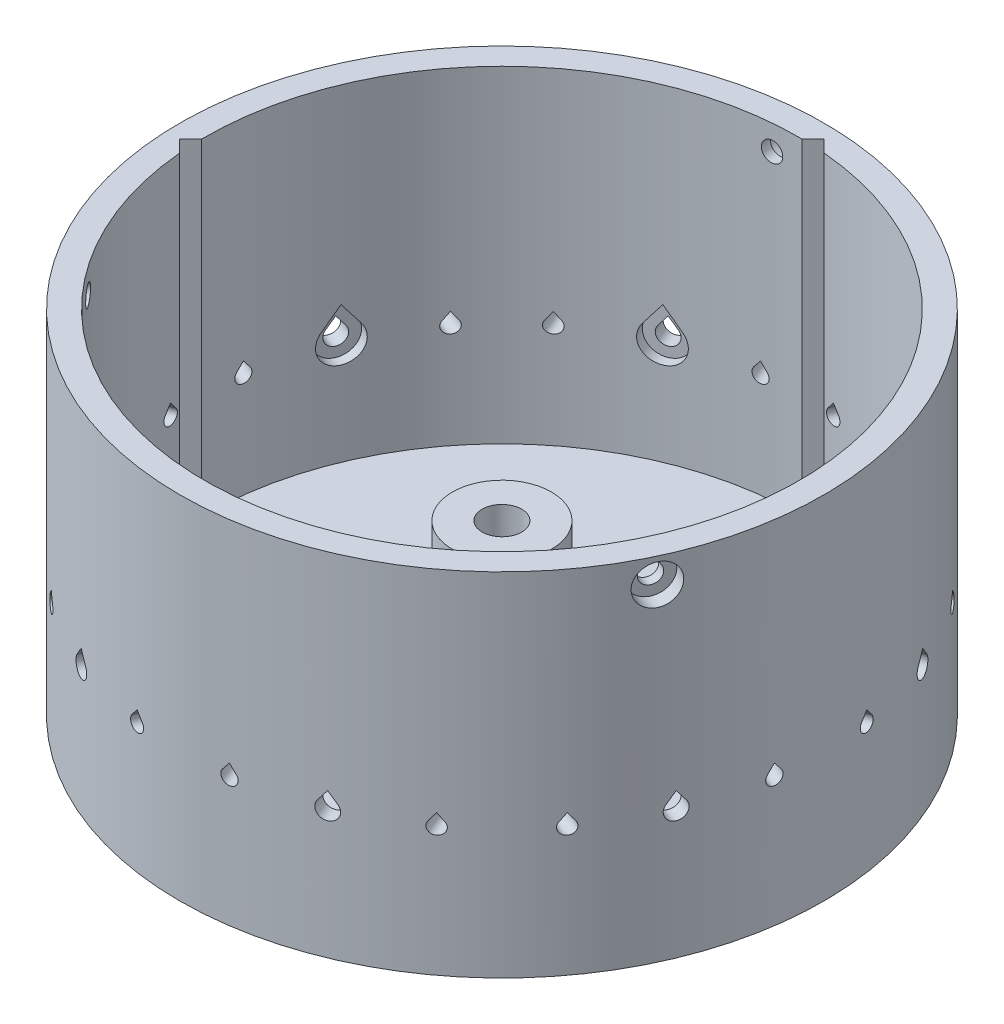
SolidWorks part; units mm, degrees
ref_plane "Front Plane" through (0, 0, 0) normal (0, 0, 1) x (1, 0, 0)
ref_plane "Top Plane" through (0, 0, 0) normal (0, 1, 0) x (1, 0, 0)
ref_plane "Right Plane" through (0, 0, 0) normal (1, 0, 0) x (0, 0, -1)
sketch "Sketch1" plane through (0, 0, 0) normal (0, 0, 1) x (1, 0, 0)
  line L0 (120, 0) -> (156, 0)
  line L1 (148, -36) -> (120, -36)
  line L2 (120, -36) -> (120, 0)
  line L3 (0, 0) -> (0, -64.9986) construction
  arc A0 (156, 0) -> (160, -4) centre (156, -4) cw
  arc A1 (160, -4) -> (151.3962, -34.1132) centre (103, -4) cw
  arc A2 (151.3962, -34.1132) -> (148, -36) centre (148, -32) cw
  dimension "D5" = 4
  dimension "D6" = 4
  dimension "D1" = 160
  dimension "D2" = 40
  dimension "D3" = 36
  dimension "D4" = 28
revolve "Revolve1" add sketch "Sketch1" angle 360 about L3
sketch "Sketch5" plane through (0, 0, 0) normal (1, 0, 0) x (0, 0, -1)
  line L0 (60, 0) -> (65, 0)
  line L1 (65, -71) -> (60, -71)
  line L2 (120, 0) -> (-120, 0) construction
  line L3 (0, 16.2431) -> (0, -72.818) construction
  line L4 (65, 0) -> (65, -31)
  line L5 (60, 0) -> (60, -71)
  line L6 (-148, -36) -> (148, -36) construction
  line L8 (65, -36) -> (65, -71)
  line L9 (65, -31) -> (81, -31)
  line L11 (65, -36) -> (81, -36)
  line L12 (81, -31) -> (81, -36)
  dimension "D1" = 65
  dimension "D2" = 5
  dimension "D3" = 90
  dimension "D4" = 35
  dimension "D5" = 5
  dimension "D6" = 16
revolve "Revolve2" add sketch "Sketch5" angle 360 about L3
sketch "Sketch6" plane through (0, 0, 0) normal (1, 0, 0) x (0, 0, -1)
  line L0 (-16, -33.5) -> (16, -33.5) construction
  line L1 (0, -33.5) -> (0, 18.5493) construction
  line L3 (-148, -36) -> (148, -36) construction
  circle A0 centre (-16, -33.5) radius 2.5
  circle A1 centre (16, -33.5) radius 2.5
  dimension "D1" = 5
  dimension "D2" = 16
extrude "Boss-Extrude1" add sketch "Sketch6" along normal up to surface and the other way up to surface
sketch "Sketch7" plane through (0, 0, 0) normal (0, 0, 1) x (1, 0, 0)
  line L0 (0, -60.0786) -> (0, 55.372) construction
pattern_circular "CirPattern2" count 4 every 45 about axis through (0, -60.0786, 0) along (0, 1, 0) of "Boss-Extrude1"
sketch "Sketch8" plane through (0, 0, 0) normal (0, 0, 1) x (1, 0, 0)
  line L0 (0, 0) -> (0, -91.6865)
  line L1 (0, -91.6865) -> (-49.5238, -91.6865)
  line L2 (-49.5238, -91.6865) -> (-60, -71)
  line L3 (-60, 0) -> (0, 0)
  line L4 (-60, 0) -> (-60, -71)
revolve "Cut-Revolve1" cut sketch "Sketch8" angle 360 about L0
sketch "Sketch9" plane through (0, -71, 0) normal (0, -1, 0) x (1, 0, 0)
  circle A0 centre (0, 0) radius 60
  circle A1 centre (0, 0) radius 60 construction
extrude "Boss-Extrude2" add sketch "Sketch9" against normal blind 5
sketch "Sketch10" plane through (0, -71, 0) normal (0, -1, 0) x (1, 0, 0)
  circle A0 centre (0, 0) radius 15
  dimension "D1" = 30
extrude "Cut-Extrude1" cut sketch "Sketch10" against normal up to next
sketch "Sketch11" plane through (0, 0, 0) normal (1, 0, 0) x (0, 0, -1)
  line L0 (0, -71) -> (0, 0) construction
  line L1 (-65, -71) -> (65, -71) construction
  line L3 (-7.3604, -71) -> (-4, -71)
  line L4 (-4, -71) -> (-4, -37)
  line L5 (-4, -37) -> (-8.0477, -37)
  line L7 (-8.0477, -37) -> (-10, -37)
  line L8 (-10, -37) -> (-10, -66)
  line L9 (-10, -66) -> (-15, -66)
  line L10 (-15, -66) -> (-15, -71)
  line L11 (-15, -71) -> (-7.3604, -71)
  line L12 (15, -66) -> (-15, -66) construction
  dimension "D1" = 34
  dimension "D3" = 20
  dimension "D4" = 8
revolve "Revolve3" add sketch "Sketch11" angle 360 about L0
sketch "Sketch14" plane through (0, 0, 0) normal (0, 1, 0) x (1, 0, 0)
  line L0 (2.8284, 62.2254) -> (-62.2254, -2.8284)
  line L1 (-62.2254, -2.8284) -> (-58.6899, -6.364)
  line L2 (-58.6899, -6.364) -> (6.364, 58.6899)
  line L3 (6.364, 58.6899) -> (2.8284, 62.2254)
  line L4 (0, 0) -> (-26.163, 26.163) construction
  line L5 (0, 0) -> (0, 27.5033) construction
  dimension "D1" = 45
  dimension "D2" = 92
  dimension "D3" = 5
  dimension "D4" = 42
extrude "Cut-Extrude3" cut sketch "Sketch14" against normal up to surface (66 mm away) up to face at (0, -66, -60)
sketch "Sketch17" plane through (0, -36, 0) normal (0, -1, 0) x (1, 0, 0)
  circle A0 centre (0, 0) radius 65
  circle A1 centre (0, 0) radius 160
  circle A2 centre (0, 0) radius 160 construction
  circle A3 centre (0, 0) radius 65 construction
extrude "Cut-Extrude4" cut sketch "Sketch17" against normal through all
ref_plane "Plane1" through (-60.0522, 0, 24.8744) normal (-0.9239, 0, 0.3827) x (0.3827, 0, 0.9239)
ref_plane "Plane2" through (-50.8134, 0, 21.0476) normal (-0.9239, 0, 0.3827) x (0.3827, 0, 0.9239)
sketch "Sketch18" plane through (-60.0522, 0, 24.8744) normal (-0.9239, 0, 0.3827) x (0.3827, 0, 0.9239)
  line L0 (65, 0) -> (-65, 0) construction
  line L1 (0, 0) -> (0, -45) construction
  line L2 (16, -45) -> (0, -45) construction
  line L3 (0, -45) -> (-16, -45) construction
  line L4 (-17.19, -44.0869) -> (-16, -42.536)
  line L5 (-16, -42.536) -> (-14.81, -44.0869)
  line L6 (-1.5867, -43.7825) -> (0, -41.7146)
  line L7 (0, -41.7146) -> (1.5867, -43.7825)
  line L8 (14.81, -44.0869) -> (16, -42.536)
  line L9 (16, -42.536) -> (17.19, -44.0869)
  line L10 (-16, -42.536) -> (-16, -45) construction
  line L11 (16, -42.536) -> (16, -45) construction
  arc A0 (-1.5867, -43.7825) -> (1.5867, -43.7825) centre (0, -45) ccw
  arc A1 (-17.19, -44.0869) -> (-14.81, -44.0869) centre (-16, -45) ccw
  arc A2 (14.81, -44.0869) -> (17.19, -44.0869) centre (16, -45) ccw
  dimension "D1" = 4
  dimension "D3" = 3
  dimension "D4" = 32
  dimension "D2" = 45
  dimension "D5" = 75
  dimension "D6" = 75
  dimension "D7" = 75
extrude "Cut-Extrude5" cut sketch "Sketch18" against normal up to next
sketch "Sketch20" plane through (-50.8134, 0, 21.0476) normal (-0.9239, 0, 0.3827) x (0.3827, 0, 0.9239)
  line L0 (-3.1734, -42.565) -> (0, -38.4293)
  line L1 (0, -38.4293) -> (3.1734, -42.565)
  line L2 (0, -45) -> (0, -38.4293) construction
  arc A0 (-3.1734, -42.565) -> (3.1734, -42.565) centre (0, -45) ccw
  dimension "D1" = 8
  dimension "D2" = 75
extrude "Cut-Extrude6" cut sketch "Sketch20" along normal blind 7
pattern_circular "CirPattern3" count 8 over 360 about axis through (0, 0, 0) along (0, 1, 0) of "Cut-Extrude5", "Cut-Extrude6"
ref_plane "Plane4" through (9.0631, 0, 4.2262) normal (0.9063, 0, 0.4226) x (0.4226, 0, -0.9063)
sketch "Sketch22" plane through (20.043, 0, -19.3204) normal (-0.9063, 0, -0.4226) x (-0.4226, 0, 0.9063)
  line L0 (25.9808, 0) -> (25.9808, -5) construction
  circle A0 centre (25.9808, -5) radius 2
  dimension "D1" = 4
  dimension "D2" = 5
extrude "Cut-Extrude8" cut sketch "Sketch22" against normal through all
ref_plane "Plane3" through (58.91, 0, 27.4702) normal (0.9063, 0, 0.4226) x (0.4226, 0, -0.9063)
sketch "Sketch23" plane through (58.91, 0, 27.4702) normal (0.9063, 0, 0.4226) x (0.4226, 0, -0.9063)
  circle A0 centre (0, -5) radius 4
  dimension "D1" = 8
extrude "Cut-Extrude9" cut sketch "Sketch23" against normal blind 3
pattern_circular "CirPattern4" count 3 over 360 about axis through (0, 0, 0) along (0, 1, 0) of "Cut-Extrude8", "Cut-Extrude9"
sketch "Sketch26" plane through (0, -71, 0) normal (0, -1, 0) x (1, 0, 0)
  line L0 (-25.9808, 15) -> (-2.2721, 15)
  line L1 (-2.2721, 15) -> (-13.8721, 26.6001)
  circle A0 centre (0, 0) radius 15 construction
  circle A1 centre (0, 0) radius 30 construction
  arc A2 (-13.8721, 26.6001) -> (-25.9808, 15) centre (0, 0) ccw
  dimension "D1" = 30
  dimension "D2" = 60
  dimension "D3" = 45
  dimension "D4" = 15
  dimension "D5" = 9
extrude "Cut-Extrude12" cut sketch "Sketch26" against normal up to next (5 mm away)
pattern_circular "CirPattern6" count 8 over 360 about axis through (0, 0, 0) along (0, 1, 0) of "Cut-Extrude12"
